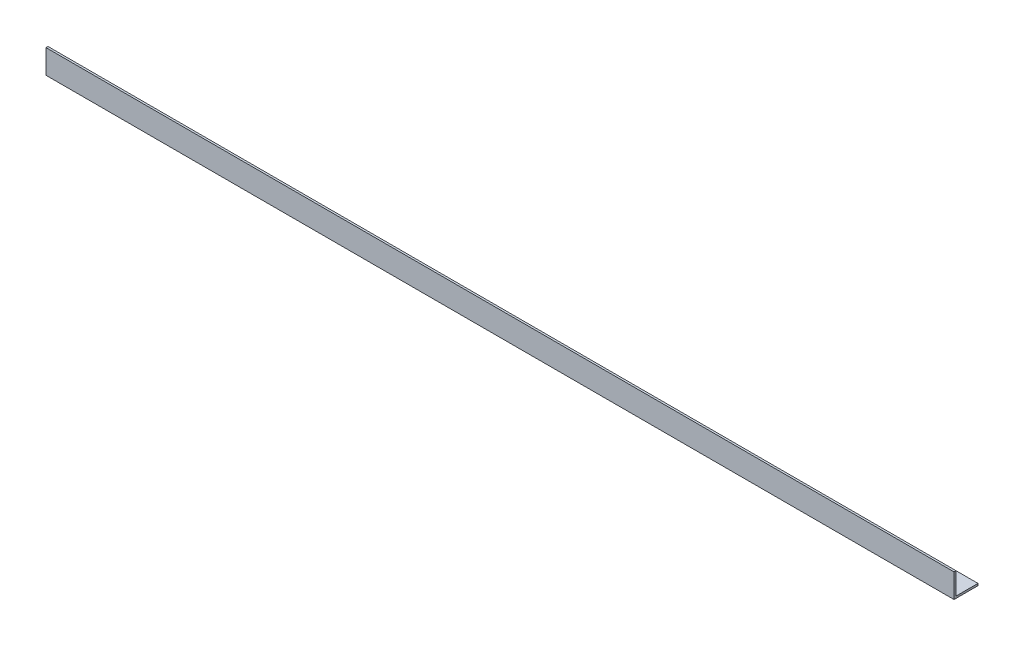
SolidWorks part; units mm, degrees
ref_plane "Front Plane" through (0, 0, 0) normal (0, 0, 1) x (1, 0, 0)
ref_plane "Top Plane" through (0, 0, 0) normal (0, 1, 0) x (1, 0, 0)
ref_plane "Right Plane" through (0, 0, 0) normal (1, 0, 0) x (0, 0, -1)
sketch "Sketch1" plane through (0, 0, 0) normal (1, 0, 0) x (0, 0, -1)
  line L0 (0, 19.05) -> (0, 0)
  line L1 (0, 0) -> (19.05, 0)
  dimension "D1" = 19.05
  dimension "D2" = 19.05
extrude "Extrude-Thin1" add sketch "Sketch1" along normal blind 720.852 thin thin type one direction reverse wall 1.5875
